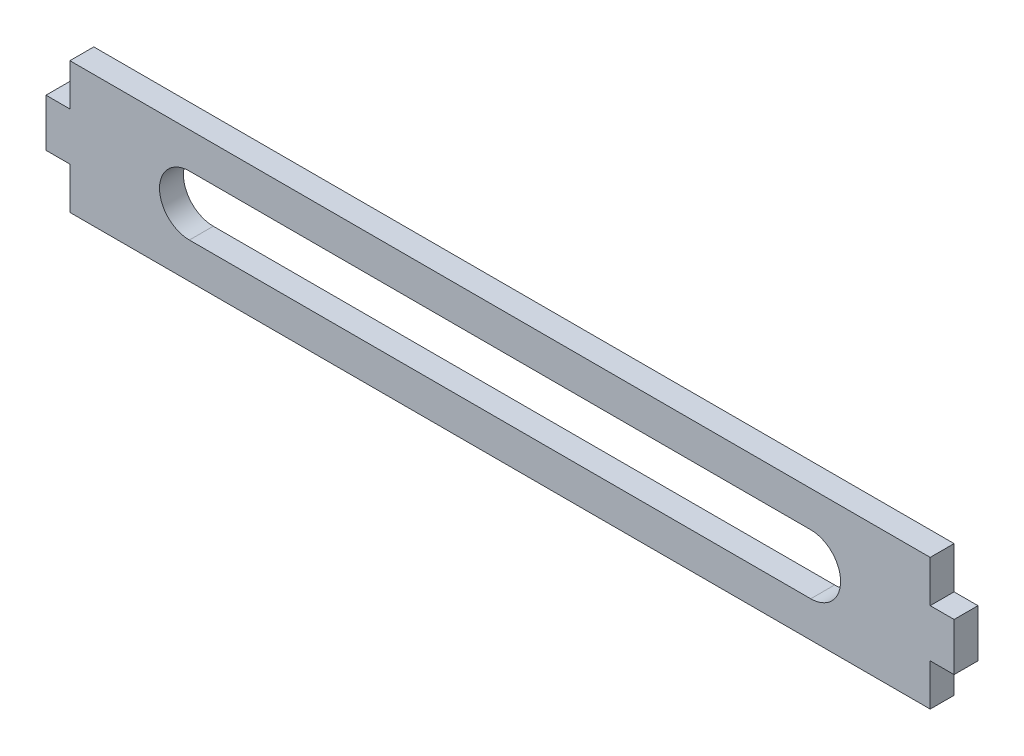
SolidWorks part; units mm, degrees
ref_plane "Front Plane" through (0, 0, 0) normal (0, 0, 1) x (1, 0, 0)
ref_plane "Top Plane" through (0, 0, 0) normal (0, 1, 0) x (1, 0, 0)
ref_plane "Right Plane" through (0, 0, 0) normal (1, 0, 0) x (0, 0, -1)
sketch "Sketch1" plane through (0, 0, 0) normal (0, 0, 1) x (1, 0, 0)
  line L0 (-114.3, 8.7301) -> (0, 8.7301) construction
  line L1 (0, 0) -> (-114.3, 0)
  line L2 (0, 0) -> (0, 5.5551)
  line L3 (0, 17.4602) -> (-114.3, 17.4602)
  line L4 (-114.3, 0) -> (-114.3, 5.5551)
  line L5 (3.175, 11.9051) -> (0, 11.9051)
  line L6 (-57.15, 17.4602) -> (-57.15, 0) construction
  line L7 (3.175, 5.5551) -> (0, 5.5551)
  line L8 (-117.475, 5.5551) -> (-114.3, 5.5551)
  line L9 (0, 11.9051) -> (0, 17.4602)
  line L13 (-114.3, 11.9051) -> (-114.3, 17.4602)
  line L14 (0, 5.5551) -> (0, 11.9051) construction
  line L15 (3.175, 11.9051) -> (3.175, 5.5551)
  line L16 (-117.475, 11.9051) -> (-117.475, 5.5551)
  line L17 (-117.475, 11.9051) -> (-114.3, 11.9051)
  point P9 (-3.175, 8.7301)
  dimension "D1" = 114.3
  dimension "D2" = 17.4602
extrude "Boss-Extrude1" add sketch "Sketch1" along normal blind 3.175
sketch "Sketch2" plane through (0, 0, 3.175) normal (0, 0, 1) x (1, 0, 0)
  line L0 (-57.15, 17.4602) -> (-57.15, 0) construction
  line L1 (0, 17.4602) -> (-114.3, 17.4602) construction
  line L2 (-114.3, 0) -> (0, 0) construction
  line L3 (-107.5813, 11.5364) -> (-101.9687, 5.9238) construction
  line L4 (-106.4588, 12.659) -> (-100.8461, 7.0463)
  line L5 (-108.7039, 10.4139) -> (-103.0912, 4.8012)
  line L6 (-117.475, 8.7301) -> (3.175, 8.7301) construction
  line L7 (-117.475, 11.9051) -> (-117.475, 5.5551) construction
  line L8 (3.175, 5.5551) -> (3.175, 11.9051) construction
  line L9 (-114.3, 17.4602) -> (-114.3, 11.9051) construction
  line L10 (-97.9293, 11.5364) -> (-92.3167, 5.9238) construction
  line L11 (-96.8068, 12.659) -> (-91.1941, 7.0463)
  line L12 (-99.0519, 10.4139) -> (-93.4392, 4.8012)
  line L13 (-88.2773, 11.5364) -> (-82.6647, 5.9238) construction
  line L14 (-87.1548, 12.659) -> (-81.5421, 7.0463)
  line L15 (-89.3999, 10.4139) -> (-83.7872, 4.8012)
  line L16 (-78.6253, 11.5364) -> (-73.0127, 5.9238) construction
  line L17 (-77.5028, 12.659) -> (-71.8901, 7.0463)
  line L18 (-79.7479, 10.4139) -> (-74.1352, 4.8012)
  line L19 (-68.9733, 11.5364) -> (-63.3607, 5.9238) construction
  line L20 (-67.8508, 12.659) -> (-62.2381, 7.0463)
  line L21 (-70.0959, 10.4139) -> (-64.4832, 4.8012)
  line L22 (-45.3267, 11.5364) -> (-50.9393, 5.9238) construction
  line L23 (-46.4492, 12.659) -> (-52.0619, 7.0463)
  line L24 (-44.2041, 10.4139) -> (-49.8168, 4.8012)
  line L25 (-35.6747, 11.5364) -> (-41.2873, 5.9238) construction
  line L26 (-36.7972, 12.659) -> (-42.4099, 7.0463)
  line L27 (-34.5521, 10.4139) -> (-40.1648, 4.8012)
  line L28 (-26.0227, 11.5364) -> (-31.6353, 5.9238) construction
  line L29 (-27.1452, 12.659) -> (-32.7579, 7.0463)
  line L30 (-24.9001, 10.4139) -> (-30.5128, 4.8012)
  line L31 (-16.3707, 11.5364) -> (-21.9833, 5.9238) construction
  line L32 (-17.4932, 12.659) -> (-23.1059, 7.0463)
  line L33 (-15.2481, 10.4139) -> (-20.8608, 4.8012)
  line L34 (-6.7187, 11.5364) -> (-12.3313, 5.9238) construction
  line L35 (-7.8412, 12.659) -> (-13.4539, 7.0463)
  line L36 (-5.5961, 10.4139) -> (-11.2088, 4.8012)
  arc A0 (-106.4588, 12.659) -> (-108.7039, 10.4139) centre (-107.5813, 11.5364) ccw
  arc A1 (-103.0912, 4.8012) -> (-100.8461, 7.0463) centre (-101.9687, 5.9238) ccw
  arc A2 (-96.8068, 12.659) -> (-99.0519, 10.4139) centre (-97.9293, 11.5364) ccw
  arc A3 (-93.4392, 4.8012) -> (-91.1941, 7.0463) centre (-92.3167, 5.9238) ccw
  arc A4 (-87.1548, 12.659) -> (-89.3999, 10.4139) centre (-88.2773, 11.5364) ccw
  arc A5 (-83.7872, 4.8012) -> (-81.5421, 7.0463) centre (-82.6647, 5.9238) ccw
  arc A6 (-77.5028, 12.659) -> (-79.7479, 10.4139) centre (-78.6253, 11.5364) ccw
  arc A7 (-74.1352, 4.8012) -> (-71.8901, 7.0463) centre (-73.0127, 5.9238) ccw
  arc A8 (-67.8508, 12.659) -> (-70.0959, 10.4139) centre (-68.9733, 11.5364) ccw
  arc A9 (-64.4832, 4.8012) -> (-62.2381, 7.0463) centre (-63.3607, 5.9238) ccw
  arc A10 (-46.4492, 12.659) -> (-44.2041, 10.4139) centre (-45.3267, 11.5364) cw
  arc A11 (-49.8168, 4.8012) -> (-52.0619, 7.0463) centre (-50.9393, 5.9238) cw
  arc A12 (-36.7972, 12.659) -> (-34.5521, 10.4139) centre (-35.6747, 11.5364) cw
  arc A13 (-40.1648, 4.8012) -> (-42.4099, 7.0463) centre (-41.2873, 5.9238) cw
  arc A14 (-27.1452, 12.659) -> (-24.9001, 10.4139) centre (-26.0227, 11.5364) cw
  arc A15 (-30.5128, 4.8012) -> (-32.7579, 7.0463) centre (-31.6353, 5.9238) cw
  arc A16 (-17.4932, 12.659) -> (-15.2481, 10.4139) centre (-16.3707, 11.5364) cw
  arc A17 (-20.8608, 4.8012) -> (-23.1059, 7.0463) centre (-21.9833, 5.9238) cw
  arc A18 (-7.8412, 12.659) -> (-5.5961, 10.4139) centre (-6.7187, 11.5364) cw
  arc A19 (-11.2088, 4.8012) -> (-13.4539, 7.0463) centre (-12.3313, 5.9238) cw
  point P8 (-104.775, 8.7301)
  point P19 (-114.3, 14.6827)
  point P26 (-95.123, 8.7301)
  point P33 (-85.471, 8.7301)
  point P40 (-75.819, 8.7301)
  point P47 (-66.167, 8.7301)
  point P52 (-48.133, 8.7301)
  point P59 (-38.481, 8.7301)
  point P66 (-28.829, 8.7301)
  point P73 (-19.177, 8.7301)
  point P80 (-9.525, 8.7301)
  dimension "D1" = 7.9375
  dimension "D2" = 3.175
  dimension "D3" = 9.525
  dimension "D4" = 5
extrude "Cut-Extrude1" [suppressed] cut sketch "Sketch2" against normal through all
sketch "Sketch3" plane through (0, 0, 3.175) normal (0, 0, 1) x (1, 0, 0)
  line L0 (-57.15, 17.4602) -> (-57.15, 0) construction
  line L1 (0, 17.4602) -> (-114.3, 17.4602) construction
  line L2 (-114.3, 0) -> (0, 0) construction
  line L3 (-15.875, 8.7301) -> (-98.425, 8.7301) construction
  line L4 (-15.875, 4.7614) -> (-98.425, 4.7614)
  line L5 (-15.875, 12.6989) -> (-98.425, 12.6989)
  arc A0 (-15.875, 4.7614) -> (-15.875, 12.6989) centre (-15.875, 8.7301) ccw
  arc A1 (-98.425, 12.6989) -> (-98.425, 4.7614) centre (-98.425, 8.7301) ccw
  point P8 (-57.15, 8.7301)
  dimension "D1" = 82.55
  dimension "D2" = 7.9375
extrude "Cut-Extrude2" cut sketch "Sketch3" against normal through all
